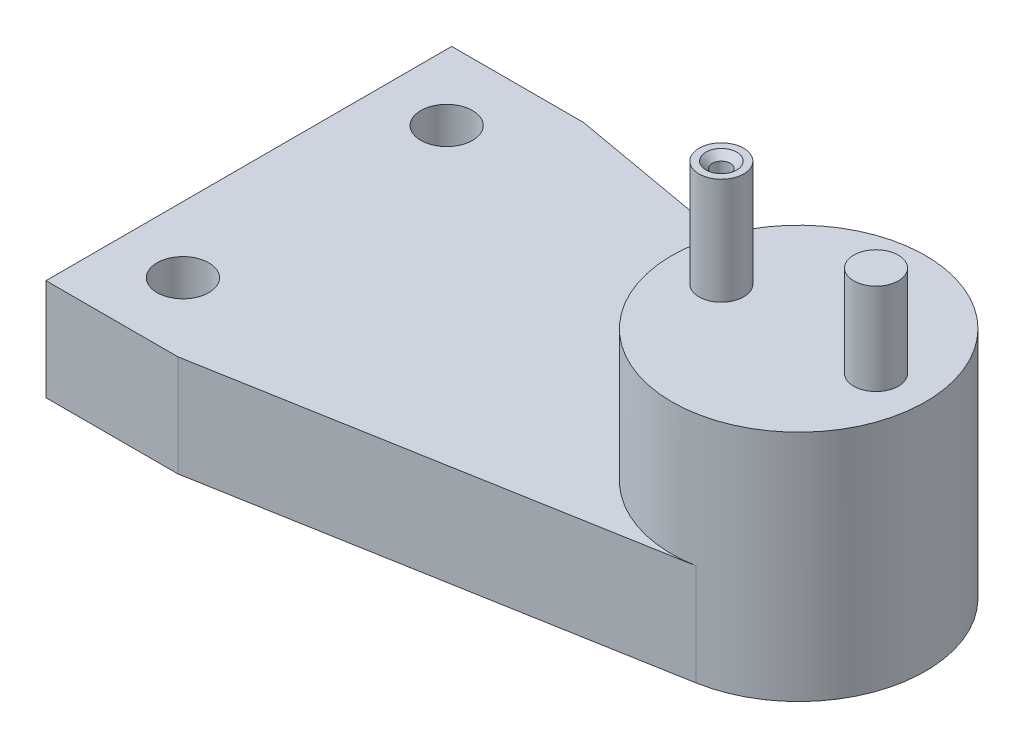
SolidWorks part; units mm, degrees
material "6061-T6 (SS)"
ref_plane "Front Plane" through (0, 0, 0) normal (0, 0, 1) x (1, 0, 0)
ref_plane "Top Plane" through (0, 0, 0) normal (0, 1, 0) x (1, 0, 0)
ref_plane "Right Plane" through (0, 0, 0) normal (1, 0, 0) x (0, 0, -1)
sketch "Sketch1" plane through (0, 0, 0) normal (0, 1, 0) x (1, 0, 0)
  line L0 (0, 0) -> (25.1136, 0) construction
  line L1 (0, 0) -> (0, -15.7184) construction
  line L2 (0, 0) -> (0, 20)
  line L3 (0, 20) -> (13, 20)
  line L4 (13, 20) -> (56.3871, 12.3081)
  line L5 (66.705, 0) -> (0, 0)
  line L6 (13, 20) -> (13, 15.7179) construction
  arc A0 (66.705, 0) -> (56.3871, 12.3081) centre (54.205, 0) ccw
  point P3 (54.205, 0)
  dimension "D3" = 25
  dimension "D1" = 13
  dimension "D2" = 41.205
  dimension "D4" = 20
extrude "Boss-Extrude1" add sketch "Sketch1" along normal blind 10
mirror "Mirror1" about plane through (66.705, 10, 0) normal (0, 0, -1) of bodies 101
sketch "Sketch2" plane through (0, 10, 0) normal (0, 1, 0) x (1, 0, 0)
  circle A0 centre (54.205, 0) radius 12.5
  arc A2 (56.3871, -12.3081) -> (56.3871, 12.3081) centre (54.205, 0) ccw construction
extrude "Boss-Extrude2" add sketch "Sketch2" along normal blind 13
hole_wizard "#10 Clearance Hole1" positions "Sketch5" profile "Sketch4" hole size "#10" standard "ANSI Inch"
sketch "Sketch5" plane through (0, 10, 0) normal (0, 1, 0) x (1, 0, 0)
  line L0 (0, 0) -> (9.4738, 0) construction
  line L1 (0, 20) -> (0, -20) construction
  line L2 (6.5, 20) -> (6.5, 15.8476) construction
  line L3 (13, 20) -> (0, 20) construction
  point P0 (6.5, 13)
  point P13 (6.5, -13)
  dimension "D1" = 13
sketch "Sketch4" plane through (6.5, 10, -13) normal (1, 0, 0) x (0, 0, 1)
  line L0 (0, 0) -> (0, 137.4238)
  line L1 (0, 137.4238) -> (2.5527, 135.89)
  line L2 (2.5527, 135.89) -> (2.5527, 0)
  line L5 (2.5527, 0) -> (0, 0)
  line L10 (0, 137.4238) -> (-2.5527, 135.89) construction
  line L11 (0, -6.35) -> (0, 107.95) construction
  dimension "Hole Dia." = 5.1054
  dimension "Hole Depth" = 135.89
  dimension "Drill Angle" = 118
sketch "Sketch6" plane through (0, 23, 0) normal (0, 1, 0) x (1, 0, 0)
  line L0 (46.58, 0) -> (61.83, 0) construction
  circle A1 centre (54.205, 0) radius 12.5 construction
  circle A2 centre (61.83, 0) radius 2.2
  circle A3 centre (46.58, 0) radius 2.2
  point P2 (54.205, 0)
  dimension "D2" = 4.4
  dimension "D1" = 15.25
extrude "Boss-Extrude3" add sketch "Sketch6" along normal blind 9
sketch "Sketch7" plane through (0, 32, 0) normal (0, 1, 0) x (1, 0, 0)
  circle A0 centre (46.58, 0) radius 2.2 construction
  circle A1 centre (46.58, 0) radius 2.2
extrude "Boss-Extrude4" add sketch "Sketch7" along normal blind 1.5
hole_wizard "#2-56 Tapped Hole1" positions "Sketch9" profile "Sketch8" tap size "#2-56" standard "ANSI Inch"
sketch "Sketch9" plane through (0, 33.5, 0) normal (0, 1, 0) x (1, 0, 0)
  circle A0 centre (46.58, 0) radius 2.2 construction
  point P0 (46.58, 0)
sketch "Sketch8" plane through (46.58, 33.5, 0) normal (1, 0, 0) x (0, 0, 1)
  line L0 (0, 0) -> (0, 7.1742)
  line L1 (0, 7.1742) -> (0.889, 6.64)
  line L2 (0.889, 6.64) -> (0.889, 0.635)
  line L3 (0.889, 0.635) -> (1.524, 0)
  line L5 (1.524, 0) -> (0, 0)
  line L6 (-0.889, 0.635) -> (-1.524, 0) construction
  line L10 (0, 7.1742) -> (-0.889, 6.64) construction
  line L11 (0, -6.35) -> (0, 107.95) construction
  dimension "Tap Drill Dia." = 1.778
  dimension "Tap Drill Depth" = 6.64
  dimension "Near C'Sink Dia." = 3.048
  dimension "Near C'Sink Angle" = 90
  dimension "Drill Angle" = 118
cosmetic thread "Hole Thread2" parameters "D1"=4.37, "D2"=2.1844
